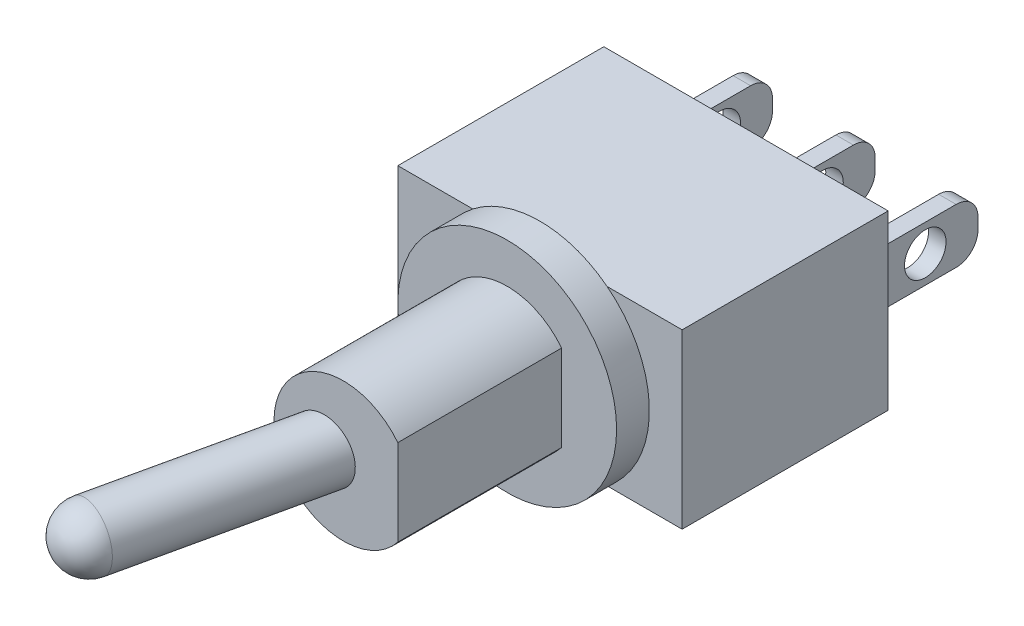
SolidWorks part; units mm, degrees
material "Nylon 101"
ref_plane "X-Y Datum" through (0, 0, 0) normal (0, 0, 1) x (1, 0, 0)
ref_plane "X-Z Datum" through (0, 0, 0) normal (0, 1, 0) x (1, 0, 0)
ref_plane "Y-Z Datum" through (0, 0, 0) normal (1, 0, 0) x (0, 0, -1)
sketch "Sketch2" plane through (0, 0, 0) normal (0, 0, 1) x (1, 0, 0)
  line L1 (6.5024, -3.9497) -> (-6.5024, -3.9497)
  line L2 (6.5024, -3.9497) -> (6.5024, 3.9497)
  line L3 (6.5024, 3.9497) -> (-6.5024, 3.9497)
  line L4 (-6.5024, -3.9497) -> (-6.5024, 3.9497)
  line L5 (6.5024, -3.9497) -> (-6.5024, 3.9497) construction
  line L6 (6.5024, 3.9497) -> (-6.5024, -3.9497) construction
  point P0 (0, 0)
  dimension "D1" = 13.0048
  dimension "D2" = 7.8994
extrude "Boss-Extrude1" add sketch "Sketch2" against normal blind 9.4234 contours L1 L4 L3 L2
sketch "Sketch5" plane through (0, 0, 0) normal (1, 0, 0) x (0, 0, -1)
  line L5 (9.4234, -3.9497) -> (9.4234, 3.9497) construction
  line L6 (9.4234, -1.25) -> (13.9352, -1.25)
  line L7 (9.4234, -1.25) -> (9.4234, 1.25)
  line L8 (9.4234, 1.25) -> (13.9352, 1.25)
  line L9 (14.9352, -0.25) -> (14.9352, 0.25)
  circle A1 centre (12.5234, 0) radius 0.95
  arc A2 (13.9352, -1.25) -> (14.9352, -0.25) centre (13.9352, -0.25) ccw
  arc A3 (13.9352, 1.25) -> (14.9352, 0.25) centre (13.9352, 0.25) cw
  point P6 (9.4234, 0)
  point P14 (14.9352, -1.25)
  point P17 (14.9352, 1.25)
  dimension "D2" = 1.9
  dimension "D5" = 1
  dimension "D1" = 2.5
  dimension "D3" = 5.5118
  dimension "D4" = 3.1
extrude "Boss-Extrude2" add sketch "Sketch5" along normal mid plane 0.8 from offset 4.7 contours A3 L8 L7 L6 A2 L9 A1
pattern_linear "LPattern1" count 3 spacing 4.7 along (-1, 0, 0) of "Boss-Extrude2"
sketch "Sketch6" plane through (0, 0, 0) normal (0, 0, 1) x (1, 0, 0)
  circle A0 centre (0, 0) radius 5.0038
  dimension "D1" = 10.0076
extrude "Boss-Extrude3" add sketch "Sketch6" along normal blind 1.4986
sketch "Sketch7" plane through (0, 0, 1.4986) normal (0, 0, 1) x (1, 0, 0)
  line L0 (2.4892, -1.9709) -> (2.4892, 1.9709)
  line L1 (0, 0) -> (3.175, 0) construction
  arc A0 (2.4892, 1.9709) -> (2.4892, -1.9709) centre (0, 0) ccw
  dimension "D1" = 6.35
  dimension "D2" = 0.6858
  dimension "D3" = 3.175
extrude "Boss-Extrude5" add sketch "Sketch7" along normal blind 7.493
sketch "Sketch8" plane through (0, 0, 0) normal (0, 1, 0) x (1, 0, 0)
  line L0 (0, -1000) -> (0, 49000) construction
  line L1 (-3.1384, -19.1479) -> (0, -4.9916)
  line L2 (3.1384, -19.1479) -> (0, -4.9916) construction
  line L4 (-3.175, -8.9916) -> (2.4892, -8.9916) construction
  line L6 (0, -4.9916) -> (-1.3639, -4.6892)
  line L7 (-1.3639, -4.6892) -> (-4.1999, -17.4816)
  arc A0 (3.1384, -19.1479) -> (-3.1384, -19.1479) centre (0, -4.9916) cw construction
  arc A1 (-4.1999, -17.4816) -> (-3.1384, -19.1479) centre (-2.836, -17.784) ccw
  point P7 (0, -4.9916)
  point P8 (0, -19.4916)
  point P15 (0, -19.4916)
  dimension "D1" = 25
  dimension "D2" = 10.5
  dimension "D3" = 4
  dimension "D4" = 1.397
  dimension "D5" = 1.397
revolve "Revolve1" add sketch "Sketch8" angle 360 about L1
